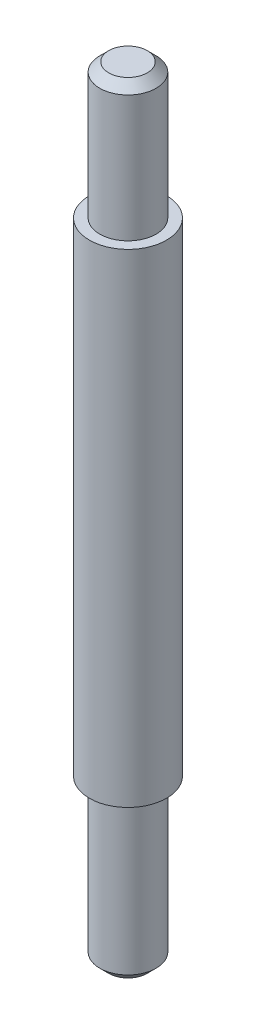
SolidWorks part; units mm, degrees
material "Malleable Cast Iron"
ref_plane "Front Plane" through (0, 0, 0) normal (0, 0, 1) x (1, 0, 0)
ref_plane "Top Plane" through (0, 0, 0) normal (0, 1, 0) x (1, 0, 0)
ref_plane "Right Plane" through (0, 0, 0) normal (1, 0, 0) x (0, 0, -1)
sketch "Sketch1" plane through (0, 0, 0) normal (0, 0, 1) x (1, 0, 0)
  line L0 (0, 127.1079) -> (0, -135.8921) construction
  line L1 (0, 127.1079) -> (6.5, 127.1079)
  line L2 (9.5, 124.1079) -> (9.5, 81.5)
  line L3 (9.5, 81.5) -> (13, 81.5)
  line L4 (13, 81.5) -> (13, -81.5)
  line L5 (13, -81.5) -> (9.5, -81.5)
  line L6 (9.5, -81.5) -> (9.5, -132.8921)
  line L7 (6.5, -135.8921) -> (0, -135.8921)
  line L8 (0, 0) -> (142.4951, 0) construction
  line L9 (0, 127.1079) -> (0, -135.8921)
  line L10 (9.5, -132.8921) -> (6.5, -135.8921)
  line L11 (6.5, 127.1079) -> (9.5, 124.1079)
  point P4 (9.5, 127.1079)
  point P10 (9.5, -135.8921)
  dimension "D1" = 263
  dimension "D2" = 163
  dimension "D3" = 13
  dimension "D4" = 9.5
  dimension "D5" = 3
  dimension "D6" = 45
  dimension "D7" = 3
  dimension "D8" = 45
revolve "Revolve1" add sketch "Sketch1" angle 360 about L9
